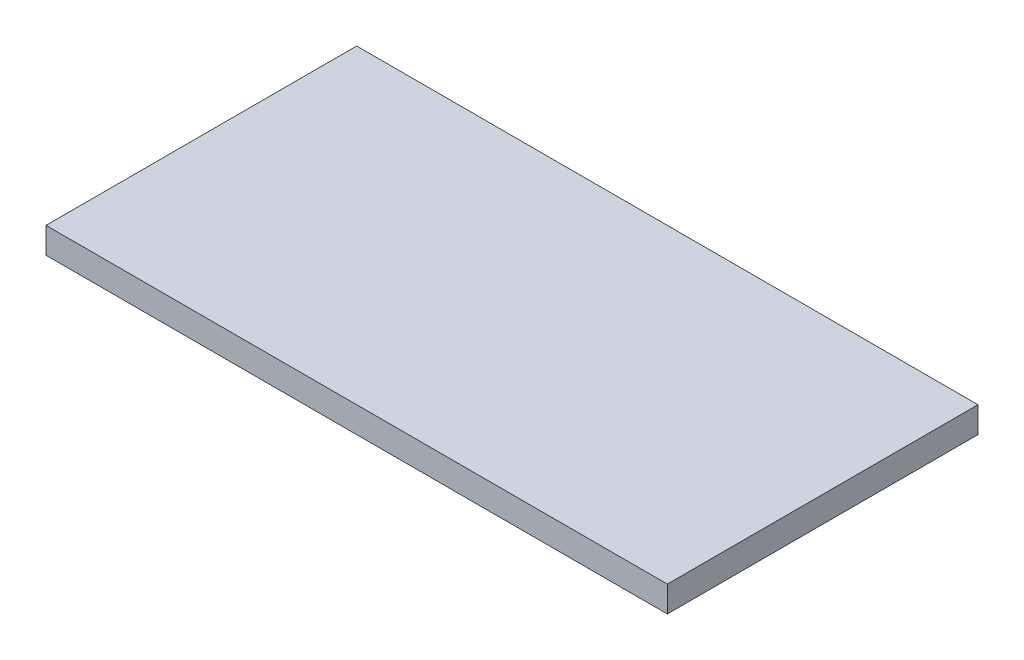
SolidWorks part; units mm, degrees
ref_plane "Front Plane" through (0, 0, 0) normal (0, 0, 1) x (1, 0, 0)
ref_plane "Top Plane" through (0, 0, 0) normal (0, 1, 0) x (1, 0, 0)
ref_plane "Right Plane" through (0, 0, 0) normal (1, 0, 0) x (0, 0, -1)
sketch "Sketch1" plane through (0, 0, 0) normal (0, 1, 0) x (1, 0, 0)
  line L1 (-55.9961, 128.8765) -> (248.8039, 128.8765)
  line L2 (-55.9961, 128.8765) -> (-55.9961, -23.5235)
  line L3 (-55.9961, -23.5235) -> (248.8039, -23.5235)
  line L4 (248.8039, 128.8765) -> (248.8039, -23.5235)
  dimension "D1" = 152.4
  dimension "D2" = 304.8
extrude "Boss-Extrude1" add sketch "Sketch1" along normal blind 12.7
